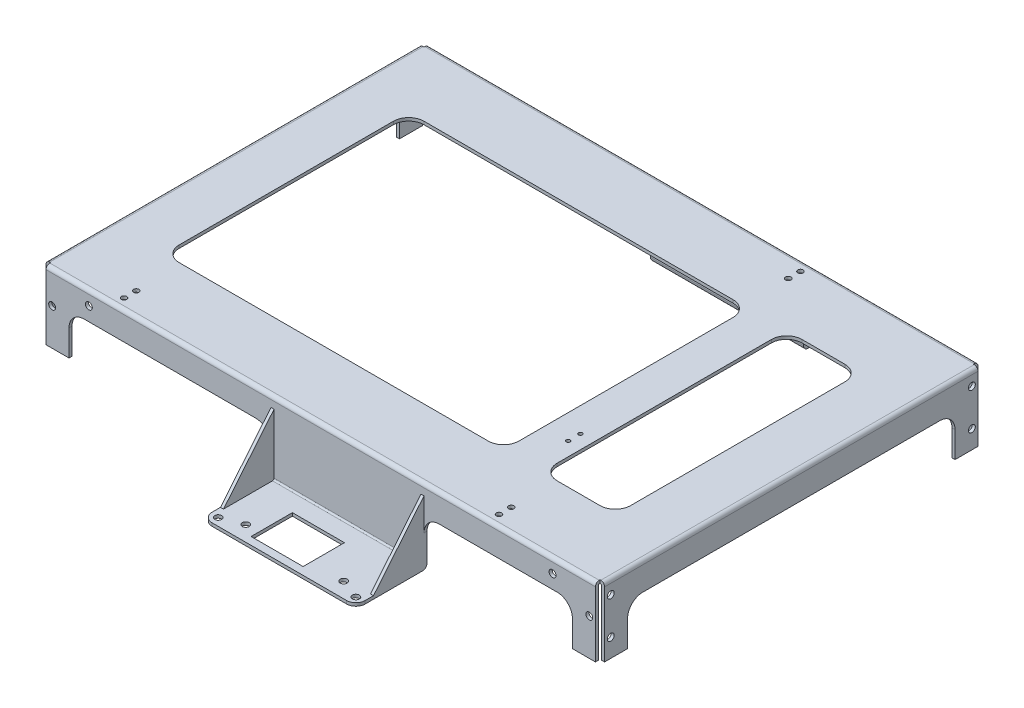
SolidWorks part; units mm, degrees
material "6061-T6 (SS)"
ref_plane "Front Plane" through (0, 0, 0) normal (0, 0, 1) x (1, 0, 0)
ref_plane "Top Plane" through (0, 0, 0) normal (0, 1, 0) x (1, 0, 0)
ref_plane "Right Plane" through (0, 0, 0) normal (1, 0, 0) x (0, 0, -1)
sketch "Sketch1" plane through (0, 0, 0) normal (1, 0, 0) x (0, 0, -1)
  line L0 (123, -45) -> (125, -45)
  line L1 (-122.5, 0) -> (122.5, 0)
  line L2 (-125, -2.5) -> (-125, -45)
  line L3 (-125, -45) -> (-123, -45)
  line L4 (125, -2.5) -> (125, -45)
  line L6 (-123, -45) -> (-123, -2.5)
  line L7 (-122.5, -2) -> (122.5, -2)
  line L8 (123, -45) -> (123, -2.5)
  arc A0 (-122.5, 0) -> (-125, -2.5) centre (-122.5, -2.5) ccw
  arc A1 (122.5, 0) -> (125, -2.5) centre (122.5, -2.5) cw
  arc A2 (122.5, -2) -> (123, -2.5) centre (122.5, -2.5) cw
  arc A3 (-123, -2.5) -> (-122.5, -2) centre (-122.5, -2.5) cw
  dimension "D1" = 2.5
  dimension "D2" = 250
  dimension "D3" = 2
  dimension "D4" = 45
extrude "Boss-Extrude1" add sketch "Sketch1" along normal mid plane 365
sketch "Sketch2" plane through (0, 0, -125) normal (0, 0, -1) x (-1, 0, 0)
  line L0 (-182.5, -45) -> (182.5, -45) construction
  line L1 (-164.5, -45) -> (164.5, -45)
  line L2 (-164.5, -45) -> (-164.5, -28)
  line L3 (-154.5, -18) -> (154.5, -18)
  line L4 (164.5, -45) -> (164.5, -28)
  line L5 (-182.5, -45) -> (-182.5, -2.5) construction
  line L6 (-182.5, 0) -> (182.5, 0) construction
  line L7 (182.5, -45) -> (182.5, -2.5) construction
  arc A0 (154.5, -18) -> (164.5, -28) centre (154.5, -28) cw
  arc A1 (-164.5, -28) -> (-154.5, -18) centre (-154.5, -28) cw
  dimension "D1" = 10
  dimension "D2" = 18
  dimension "D3" = 18
  dimension "D4" = 18
extrude "Cut-Extrude1" cut sketch "Sketch2" against normal through all
sketch "Sketch3" plane through (0, 0, 0) normal (1, 0, 0) x (0, 0, -1)
  line L0 (-123, -45) -> (-123, -2.5) construction
  line L1 (-169.5, -47) -> (-126, -47)
  line L2 (-169.5, -47) -> (-169.5, -49)
  line L3 (-169.5, -49) -> (-126, -49)
  line L4 (-123, -18) -> (-123, -46)
  line L5 (123, -2.5) -> (123, -45) construction
  line L6 (126, -47) -> (169.5, -47)
  line L7 (123, -18) -> (123, -46)
  line L8 (126, -49) -> (169.5, -49)
  line L9 (169.5, -47) -> (169.5, -49)
  line L10 (-125, -18) -> (-123, -18) construction
  line L11 (-125, -18) -> (-123, -18)
  line L12 (123, -18) -> (125, -18) construction
  line L13 (123, -18) -> (125, -18)
  line L14 (125, -18) -> (125, -46)
  line L15 (122.5, 0) -> (-122.5, 0) construction
  line L17 (-125, -18) -> (-125, -46)
  arc A0 (126, -49) -> (123, -46) centre (126, -46) cw
  arc A1 (125, -46) -> (126, -47) centre (126, -46) ccw
  arc A2 (-125, -46) -> (-126, -47) centre (-126, -46) cw
  arc A3 (-126, -49) -> (-123, -46) centre (-126, -46) ccw
  point P28 (-123, -49)
  dimension "D1" = 3
  dimension "D2" = 47
  dimension "D3" = 339
extrude "Boss-Extrude2" add sketch "Sketch3" along normal mid plane 100 from offset 17.5
sketch "Sketch4" plane through (-32.5, 0, 0) normal (-1, 0, 0) x (0, 0, 1)
  line L0 (125, -7) -> (158, -47)
  line L1 (125, -2.5) -> (125, -45) construction
  line L2 (126, -47) -> (169.5, -47) construction
  line L3 (158, -47) -> (125, -47)
  line L4 (125, -47) -> (125, -7)
  line L5 (-125, -7) -> (-158, -47)
  line L6 (-125, -45) -> (-125, -2.5) construction
  line L7 (-169.5, -47) -> (-126, -47) construction
  line L8 (-158, -47) -> (-125, -47)
  line L9 (-125, -47) -> (-125, -7)
  dimension "D1" = 40
  dimension "D2" = 33
extrude "Boss-Extrude3" add sketch "Sketch4" against normal blind 2
ref_plane "Plane1" through (17.5, 0, 0) normal (1, 0, 0) x (0, 0, -1)
mirror "Mirror1" about plane through (17.5, 0, 0) normal (1, 0, 0) of "Boss-Extrude3"
sketch "Sketch5" plane through (0, -49, 0) normal (0, -1, 0) x (1, 0, 0)
  line L0 (2, -133) -> (33, -164) construction
  line L1 (-32.5, -126) -> (-32.5, -169.5) construction
  line L2 (67.5, -169.5) -> (-32.5, -169.5) construction
  line L4 (-6, 164.5) -> (28, 164.5)
  line L5 (-6, 164.5) -> (-6, 137.5)
  line L6 (-6, 137.5) -> (28, 137.5)
  line L7 (28, 164.5) -> (28, 137.5)
  line L8 (67.5, 169.5) -> (-32.5, 169.5) construction
  line L9 (-5, 139.5) -> (-5, 163.767) construction
  circle A0 centre (17.5, -148.5) radius 11.25
  circle A1 centre (2, -133) radius 2.25
  circle A2 centre (2, -164) radius 2.25
  circle A3 centre (33, -164) radius 2.25
  circle A4 centre (33, -133) radius 2.25
  circle A5 centre (-27.5, -164.5) radius 2.25
  circle A6 centre (-14.5, -141.85) radius 2.25
  circle A7 centre (49.5, -141.85) radius 2.25
  circle A8 centre (-27.5, 164.5) radius 2.25
  circle A9 centre (-14.5, 159.5) radius 2.25
  circle A10 centre (49.5, 159.5) radius 2.25
  circle A11 centre (62.5, -164.5) radius 2.25
  circle A12 centre (62.5, 164.5) radius 2.25
  dimension "D3" = 22.5
  dimension "D4" = 4.5
  dimension "D6" = 4.5
  dimension "D1" = 31
  dimension "D2" = 31
  dimension "D5" = 21
  dimension "D7" = 5
  dimension "D8" = 34
  dimension "D9" = 32
  dimension "D10" = 1
  dimension "D11" = 50
extrude "Cut-Extrude2" cut sketch "Sketch5" against normal blind 2
fillet "Fillet1" radius 10 4 edges at (67.5, -18, -124) (67.5, -18, 124) (-32.5, -18, -124) (-32.5, -18, 124)
sketch "Sketch7" plane through (0, -2, 0) normal (0, -1, 0) x (1, 0, 0)
  line L0 (-164.5, -123) -> (-182.5, -123) construction
  line L1 (-182.5, 123) -> (-180.5, 123)
  line L2 (-182.5, 123) -> (-182.5, -123)
  line L3 (-182.5, -123) -> (-180.5, -123)
  line L4 (-180.5, 123) -> (-180.5, -123)
  line L6 (182.5, 123) -> (180.5, 123)
  line L7 (182.5, 123) -> (182.5, -123)
  line L8 (182.5, -123) -> (180.5, -123)
  line L9 (180.5, 123) -> (180.5, -123)
  dimension "D1" = 2
extrude "Boss-Extrude4" add sketch "Sketch7" along normal up to surface (43 mm away) up to face at (-173.5, -45, 124)
sketch "Sketch8" plane through (0, -45, 0) normal (0, -1, 0) x (1, 0, 0)
  line L1 (-182.5, 125) -> (-179.5, 125)
  line L2 (-182.5, 125) -> (-182.5, 122)
  line L3 (-182.5, 122) -> (-179.5, 122)
  line L4 (-179.5, 125) -> (-179.5, 122)
  line L5 (-182.5, -125) -> (-179.5, -125)
  line L6 (-182.5, -125) -> (-182.5, -122)
  line L7 (-182.5, -122) -> (-179.5, -122)
  line L8 (-179.5, -125) -> (-179.5, -122)
  line L9 (182.5, -125) -> (179.5, -125)
  line L10 (182.5, -125) -> (182.5, -122)
  line L11 (182.5, -122) -> (179.5, -122)
  line L12 (179.5, -125) -> (179.5, -122)
  line L13 (182.5, 125) -> (179.5, 125)
  line L14 (182.5, 125) -> (182.5, 122)
  line L15 (182.5, 122) -> (179.5, 122)
  line L16 (179.5, 125) -> (179.5, 122)
  dimension "D1" = 3
extrude "Cut-Extrude4" cut sketch "Sketch8" against normal through all
fillet "Fillet2" radius 0.5 2 edges at (180.5, -2, 0) (-180.5, -2, 0)
fillet "Fillet3" radius 2.5 2 edges at (182.5, 0, 0) (-182.5, 0, 0)
sketch "Sketch9" plane through (-182.5, 0, 0) normal (-1, 0, 0) x (0, 0, 1)
  line L0 (122, -45) -> (-122, -45) construction
  line L1 (-107, -45) -> (107, -45)
  line L2 (-107, -45) -> (-107, -28)
  line L3 (-97, -18) -> (97, -18)
  line L4 (107, -45) -> (107, -28)
  line L5 (-125, -2.5) -> (-125, -45) construction
  line L6 (125, -2.5) -> (125, -45) construction
  line L7 (-122, 0) -> (122, 0) construction
  arc A0 (97, -18) -> (107, -28) centre (97, -28) cw
  arc A1 (-107, -28) -> (-97, -18) centre (-97, -28) cw
  dimension "D1" = 10
  dimension "D2" = 18
  dimension "D3" = 18
  dimension "D4" = 18
extrude "Cut-Extrude5" cut sketch "Sketch9" against normal through all
sketch "Sketch10" plane through (0, 0, 125) normal (0, 0, 1) x (1, 0, 0)
  circle A1 centre (-175.5, -21) radius 2.25
  circle A2 centre (-151.5, -9) radius 2.25
  circle A3 centre (151.5, -9) radius 2.25
  circle A4 centre (175.5, -21) radius 2.25
  dimension "D1" = 4.5
extrude "Cut-Extrude6" cut sketch "Sketch10" against normal through all
sketch "Sketch11" plane through (-182.5, 0, 0) normal (-1, 0, 0) x (0, 0, 1)
  circle A0 centre (-118, -9) radius 2.25
  circle A1 centre (-118, -33) radius 2.25
  circle A2 centre (118, -9) radius 2.25
  circle A3 centre (118, -33) radius 2.25
  dimension "D1" = 4.5
extrude "Cut-Extrude7" cut sketch "Sketch11" against normal through all
sketch "Sketch12" plane through (0, -2, 0) normal (0, -1, 0) x (1, 0, 0)
  line L0 (-154.5, -125) -> (-42.5, -125) construction
  line L1 (109.5, 80) -> (137.5, 80)
  line L2 (99.5, 70) -> (99.5, -70)
  line L3 (109.5, -80) -> (137.5, -80)
  line L4 (147.5, 70) -> (147.5, -70)
  line L5 (-154.5, 125) -> (-42.5, 125) construction
  line L7 (182.5, 97) -> (182.5, -97) construction
  line L8 (-182.5, 97) -> (-182.5, -97) construction
  line L9 (-137.5, 80) -> (64.5, 80)
  line L10 (-147.5, 70) -> (-147.5, -70)
  line L11 (-137.5, -80) -> (64.5, -80)
  line L12 (74.5, 70) -> (74.5, -70)
  arc A0 (99.5, -70) -> (109.5, -80) centre (109.5, -70) ccw
  arc A1 (109.5, 80) -> (99.5, 70) centre (109.5, 70) ccw
  arc A2 (137.5, 80) -> (147.5, 70) centre (137.5, 70) cw
  arc A3 (137.5, -80) -> (147.5, -70) centre (137.5, -70) ccw
  arc A4 (64.5, 80) -> (74.5, 70) centre (64.5, 70) cw
  arc A5 (-137.5, 80) -> (-147.5, 70) centre (-137.5, 70) ccw
  arc A6 (-147.5, -70) -> (-137.5, -80) centre (-137.5, -70) ccw
  arc A7 (64.5, -80) -> (74.5, -70) centre (64.5, -70) ccw
  dimension "D1" = 10
  dimension "D4" = 10
  dimension "D2" = 45
  dimension "D3" = 45
  dimension "D5" = 35
  dimension "D6" = 35
  dimension "D7" = 25
  dimension "D8" = 83
extrude "Cut-Extrude8" cut sketch "Sketch12" against normal through all
sketch "Sketch14" plane through (0, 0, -125) normal (0, 0, -1) x (-1, 0, 0)
  line L0 (-182.5, -2.5) -> (-182.5, -45) construction
  line L1 (182.5, -2.5) -> (182.5, -45) construction
  line L2 (-179.5, 0) -> (179.5, 0) construction
  line L3 (-65.5, -46) -> (-65.5, -7) construction
  circle A0 centre (-112.5, -10) radius 3.5
  circle A1 centre (112.5, -10) radius 3.5
  circle A2 centre (-51.5, -11) radius 8
  dimension "D1" = 7
  dimension "D7" = 16
  dimension "D2" = 70
  dimension "D3" = 70
  dimension "D4" = 10
  dimension "D5" = 11
  dimension "D6" = 14
extrude "Cut-Extrude9" cut sketch "Sketch14" against normal blind 10
fillet "Fillet4" radius 6 4 edges at (-32.5, -48, 169.5) (67.5, -48, 169.5) (-32.5, -48, -169.5) (67.5, -48, -169.5)
sketch "Sketch15" plane through (0, 0, 0) normal (0, 1, 0) x (1, 0, 0)
  line L0 (179.5, -125) -> (-179.5, -125) construction
  line L1 (182.5, 122) -> (182.5, -122) construction
  line L2 (-182.5, -122) -> (-182.5, 122) construction
  line L3 (179.5, 125) -> (-179.5, 125) construction
  circle A0 centre (109.5, -118) radius 1.75
  circle A1 centre (109.5, -110) radius 1.75
  circle A2 centre (-135.5, -118) radius 1.75
  circle A3 centre (-135.5, -110) radius 1.75
  circle A4 centre (70.5, 110) radius 1.75
  circle A5 centre (70.5, 118) radius 1.75
  circle A6 centre (90.5, -53.8) radius 1.25
  circle A7 centre (90.5, -45.8) radius 1.25
  dimension "D4" = 3.5
  dimension "D11" = 2.5
  dimension "D1" = 7
  dimension "D2" = 73
  dimension "D3" = 8
  dimension "D5" = 47
  dimension "D6" = 7
  dimension "D7" = 8
  dimension "D8" = 112
  dimension "D9" = 8
  dimension "D10" = 92
  dimension "D12" = 71.2
extrude "Cut-Extrude10" cut sketch "Sketch15" against normal blind 10
